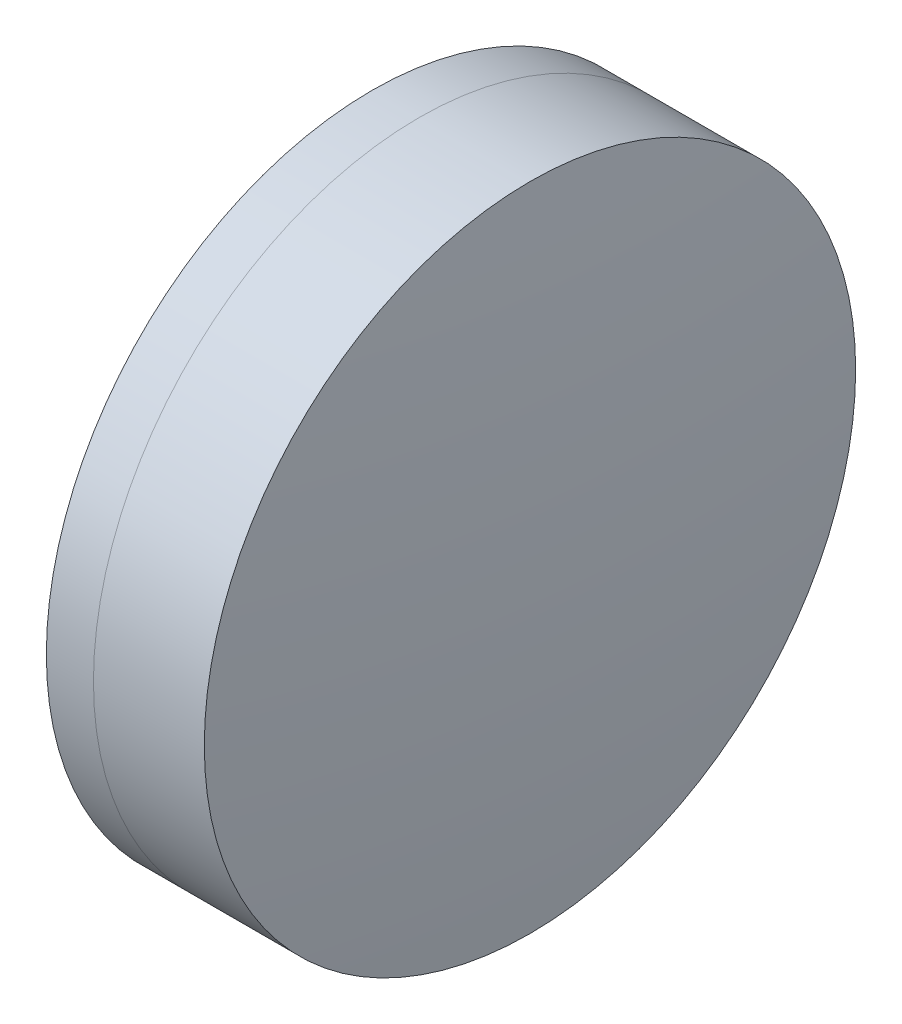
SolidWorks part; units mm, degrees
ref_plane "前视基准面" through (0, 0, 0) normal (0, 0, 1) x (1, 0, 0)
ref_plane "上视基准面" through (0, 0, 0) normal (0, 1, 0) x (1, 0, 0)
ref_plane "右视基准面" through (0, 0, 0) normal (1, 0, 0) x (0, 0, -1)
sketch "草图1" plane through (0, 0, 0) normal (0, 1, 0) x (1, 0, 0)
  line L0 (124.5233, 0) -> (646.9917, 0) construction
  line L1 (286.5256, -12.7) -> (288.3623, -12.7)
  line L2 (286.5256, 12.7) -> (288.3623, 12.7)
  arc A0 (288.3623, -12.7) -> (288.3623, 12.7) centre (264.479, 0) ccw
  arc A1 (286.5256, 12.7) -> (286.5256, -12.7) centre (317.579, 0) ccw
  point P10 (284.029, 0)
  point P11 (291.529, 0)
  dimension "D3" = 33.55
  dimension "D4" = 27.05
  dimension "D1" = 12.7
  dimension "D2" = 12.7
  dimension "D5" = 7.5
revolve "旋转1" add sketch "草图1" angle 360 about L0
sketch "草图2" plane through (0, 0, 0) normal (0, 1, 0) x (1, 0, 0)
  line L0 (-0.5519, 0) -> (622.6607, 0) construction
  line L2 (288.3623, 12.7) -> (292.6853, 12.7)
  line L3 (288.3623, -12.7) -> (292.6853, -12.7)
  arc A0 (292.6853, -12.7) -> (292.6853, 12.7) centre (167.729, 0) ccw
  arc A1 (288.3623, -12.7) -> (288.3623, 12.7) centre (264.479, 0) ccw construction
  arc A2 (288.3623, -12.7) -> (288.3623, 12.7) centre (264.479, 0) ccw
  point P4 (291.529, 0)
  point P8 (293.329, 0)
  dimension "D1" = 125.6
  dimension "D2" = 1.8
revolve "旋转3" add sketch "草图2" angle 360 about L0
